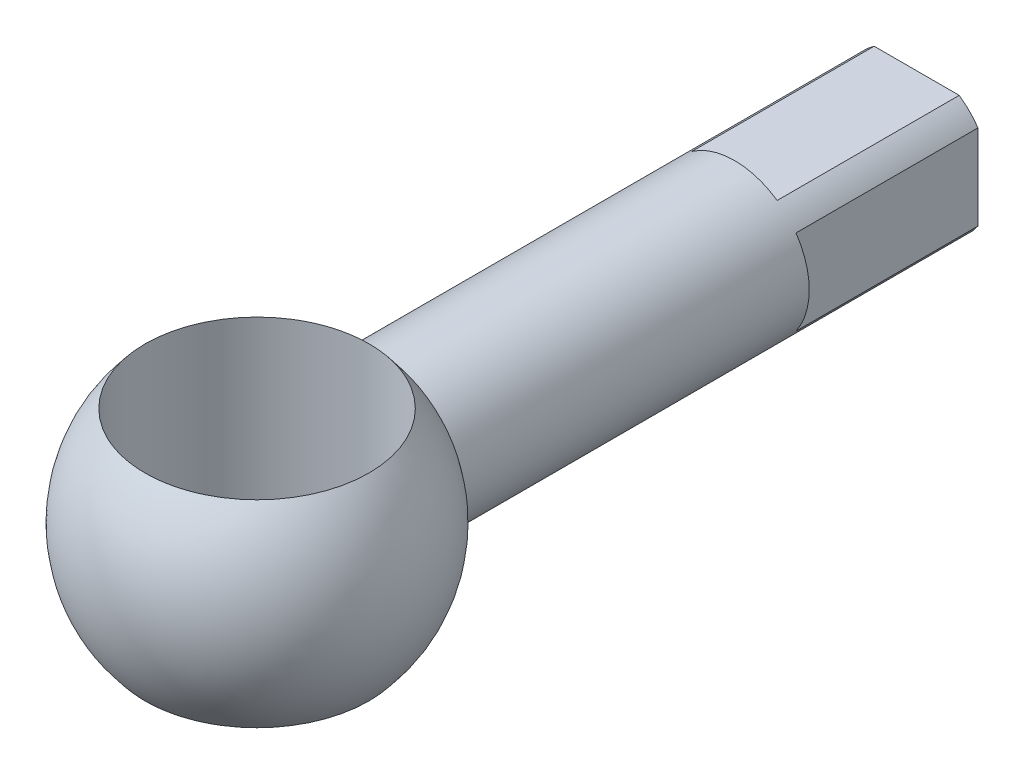
SolidWorks part; units mm, degrees
ref_plane "Front Plane" through (0, 0, 0) normal (0, 0, 1) x (1, 0, 0)
ref_plane "Top Plane" through (0, 0, 0) normal (0, 1, 0) x (1, 0, 0)
ref_plane "Right Plane" through (0, 0, 0) normal (1, 0, 0) x (0, 0, -1)
sketch "Sketch2" plane through (0, 0, 0) normal (0, 1, 0) x (1, 0, 0)
  line L0 (0, 52.4446) -> (0, -77.6253) construction
  line L1 (0, -64.8705) -> (0, 72.7975)
  line L2 (0, 72.7975) -> (-12.7, 72.7975)
  line L3 (-12.7, 72.7975) -> (-12.7, -17.4735)
  arc A0 (-12.7, -17.4735) -> (0, -64.8705) centre (0, -39.4705) ccw
  point P4 (0, -36.0497)
  point P7 (0, -77.6253)
  point P11 (0, -62.6265)
  dimension "D1" = 12.7
  dimension "D2" = 112.268
  dimension "D3" = 50.8
revolve "Revolve2" add sketch "Sketch2" angle 360 about L0
sketch "Sketch3" plane through (0, 0, 0) normal (0, 1, 0) x (1, 0, 0)
  circle A0 centre (0, -39.4705) radius 19.05
  arc A1 (-12.7, -17.4735) -> (12.7, -17.4735) centre (0, -39.4705) ccw construction
  dimension "D1" = 0
  dimension "D2" = 38.1
extrude "Cut-Extrude1" cut sketch "Sketch3" against normal through all both and the other way through all
sketch "Sketch4" plane through (0, 0, -72.7975) normal (0, 0, -1) x (-1, 0, 0)
  line L0 (-7.239, -10.4349) -> (7.239, -10.4349)
  line L1 (10.4349, 7.239) -> (10.4349, -7.239)
  line L2 (0, 15.488) -> (0, -13.7957) construction
  line L3 (-18.4953, 0) -> (22.0209, 0) construction
  line L4 (-10.4349, 7.239) -> (-10.4349, -7.239)
  line L5 (-7.239, 10.4349) -> (7.239, 10.4349)
  circle A0 centre (0, 0) radius 12.7 construction
  circle A1 centre (0, 0) radius 12.7 construction
  arc A2 (-10.4349, 7.239) -> (-10.4349, -7.239) centre (0, 0) ccw
  arc A3 (7.239, 10.4349) -> (-7.239, 10.4349) centre (0, 0) ccw
  arc A4 (10.4349, -7.239) -> (10.4349, 7.239) centre (0, 0) ccw
  arc A5 (-7.239, -10.4349) -> (7.239, -10.4349) centre (0, 0) ccw
  dimension "D1" = 14.478
  dimension "D2" = 14.478
extrude "Cut-Extrude2" cut sketch "Sketch4" against normal blind 30.988
